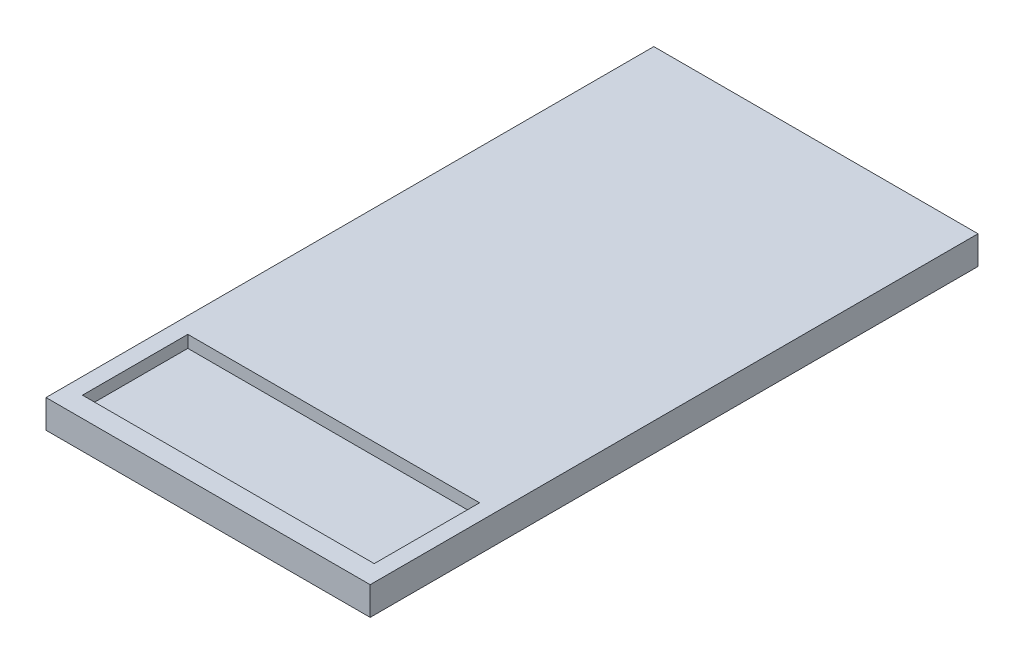
SolidWorks part; units mm, degrees
material "Acrylic (Medium-high impact)"
ref_plane "Front Plane" through (0, 0, 0) normal (0, 0, 1) x (1, 0, 0)
ref_plane "Top Plane" through (0, 0, 0) normal (0, 1, 0) x (1, 0, 0)
ref_plane "Right Plane" through (0, 0, 0) normal (1, 0, 0) x (0, 0, -1)
sketch "Sketch1" plane through (0, 0, 0) normal (0, 1, 0) x (1, 0, 0)
  line L1 (-40, 75) -> (40, 75)
  line L2 (-40, 75) -> (-40, -75)
  line L3 (-40, -75) -> (40, -75)
  line L4 (40, 75) -> (40, -75)
  dimension "D1" = 150
  dimension "D2" = 75
  dimension "D3" = 80
  dimension "D4" = 40
extrude "Extrude1" add sketch "Sketch1" against normal blind 7
sketch "Sketch3" plane through (0, 0, 0) normal (0, 1, 0) x (1, 0, 0)
  line L1 (-36, -44) -> (36, -44)
  line L2 (-36, -44) -> (-36, -70)
  line L3 (-36, -70) -> (36, -70)
  line L4 (36, -44) -> (36, -70)
  line L5 (-40, -75) -> (40, -75) construction
  point P4 (0, -70)
  dimension "D1" = 72
  dimension "D2" = 26
  dimension "D3" = 31
extrude "Extrude2" cut sketch "Sketch3" against normal blind 3
